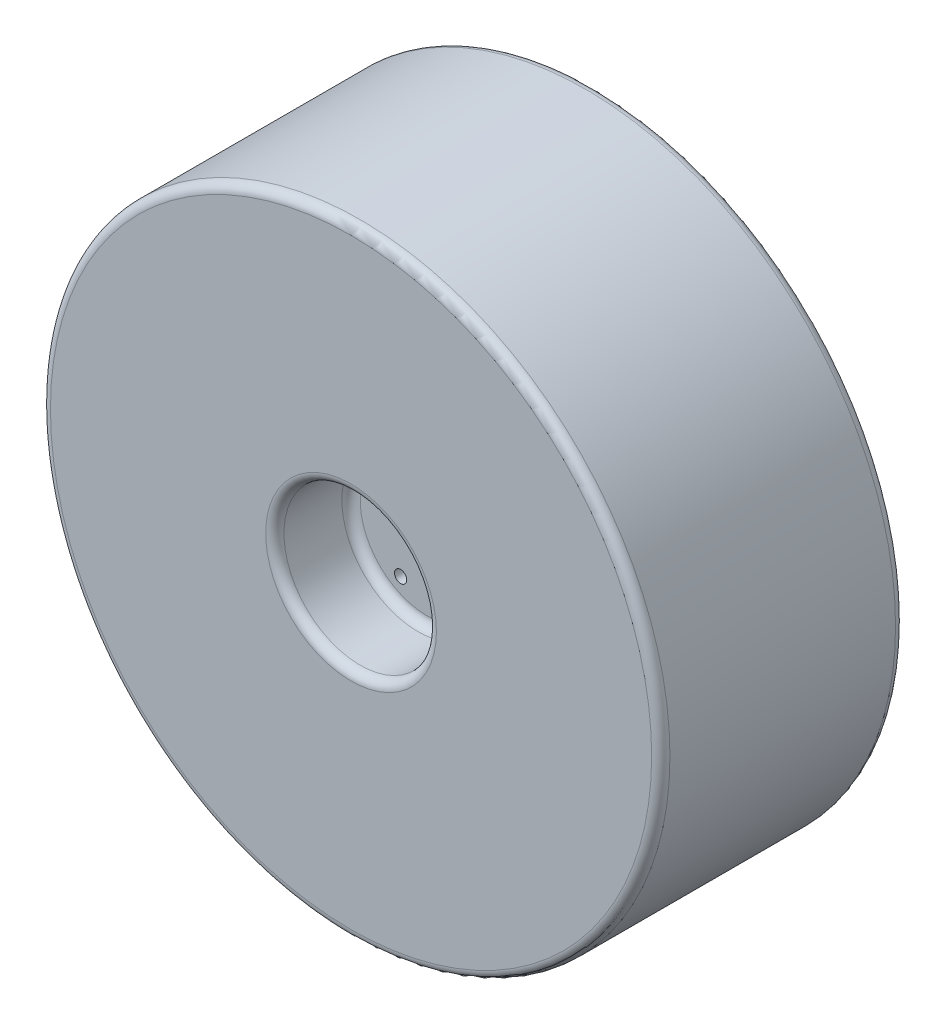
SolidWorks part; units mm, degrees
ref_plane "Front Plane" through (0, 0, 0) normal (0, 0, 1) x (1, 0, 0)
ref_plane "Top Plane" through (0, 0, 0) normal (0, 1, 0) x (1, 0, 0)
ref_plane "Right Plane" through (0, 0, 0) normal (1, 0, 0) x (0, 0, -1)
sketch "Sketch1" plane through (0, 0, 0) normal (0, 0, 1) x (1, 0, 0)
  circle A1 centre (0, 0) radius 203.2
  dimension "D1" = 406.4
extrude "Boss-Extrude2" add sketch "Sketch1" along normal blind 160
sketch "Sketch3" plane through (0, 0, 160) normal (0, 0, 1) x (1, 0, 0)
  circle A0 centre (0, 0) radius 50
extrude "Cut-Extrude1" cut sketch "Sketch3" against normal blind 50
sketch "Sketch4" plane through (0, 0, 0) normal (0, 0, -1) x (-1, 0, 0)
  circle A0 centre (0, 0) radius 50
extrude "Cut-Extrude2" cut sketch "Sketch4" against normal blind 50
fillet "Fillet1" radius 6 6 edges at (50, 0, 160) (50, 0, 110) (-50, 0, 0) (203.2, 0, 0) (203.2, 0, 160) (-50, 0, 50)
sketch "Sketch5" plane through (0, 0, 110) normal (0, 0, 1) x (1, 0, 0)
  line L0 (0, 0) -> (44, 0) construction
  circle A0 centre (0, 0) radius 44 construction
  circle A1 centre (35, 0) radius 4
  circle A2 centre (-17.5, -30.3109) radius 4
  circle A3 centre (-17.5, 30.3109) radius 4
  point P5 (35, 0)
  point P14 (0, 0)
  point P15 (0, 0)
  dimension "D1" = 35
  dimension "D2" = 8
  dimension "D3" = 3
extrude "Cut-Extrude3" cut sketch "Sketch5" against normal blind 45
sketch "Sketch6" plane through (0, 0, 110) normal (0, 0, 1) x (1, 0, 0)
  circle A0 centre (0, 0) radius 6.5
  dimension "D1" = 13
extrude "Cut-Extrude4" cut sketch "Sketch6" against normal through all
